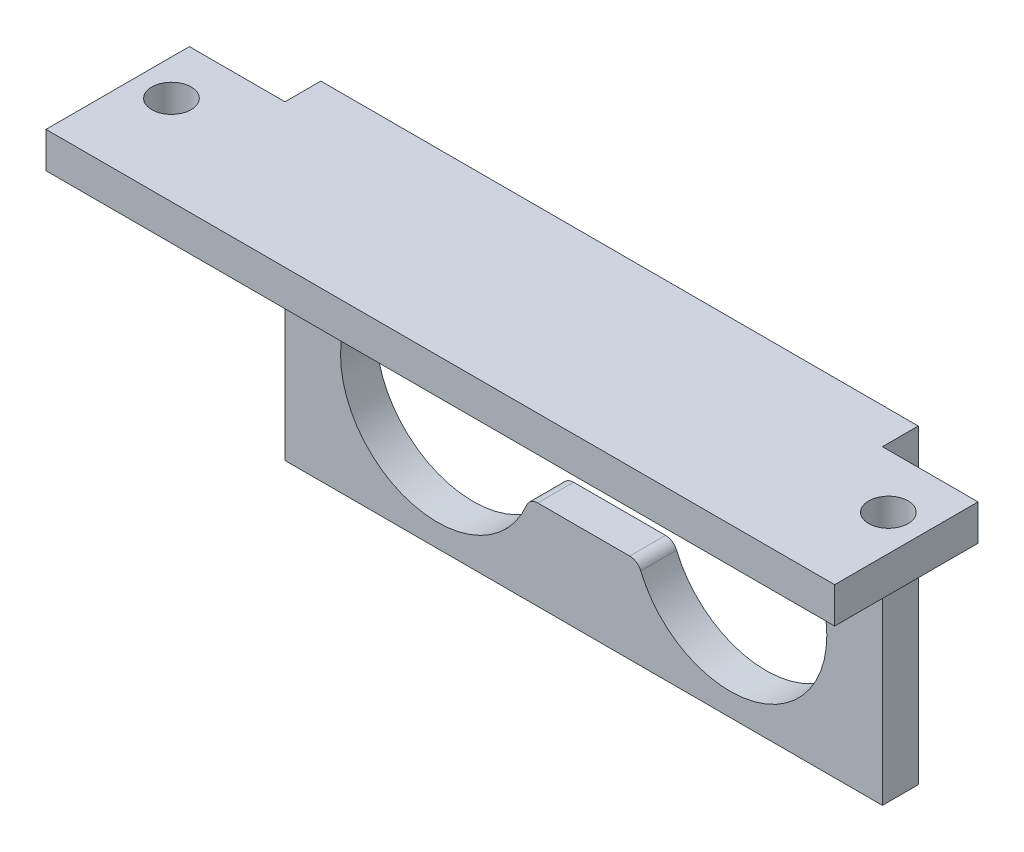
SolidWorks part; units mm, degrees
ref_plane "前视基准面" through (0, 0, 0) normal (0, 0, 1) x (1, 0, 0)
ref_plane "上视基准面" through (0, 0, 0) normal (0, 1, 0) x (1, 0, 0)
ref_plane "右视基准面" through (0, 0, 0) normal (1, 0, 0) x (0, 0, -1)
sketch "草图1" plane through (0, 0, 0) normal (0, 0, 1) x (1, 0, 0)
  line L1 (25, -10) -> (-25, -10)
  line L2 (25, -10) -> (25, 10)
  line L3 (25, 10) -> (-25, 10)
  line L4 (-25, -10) -> (-25, 10)
  line L5 (25, -10) -> (-25, 10) construction
  line L6 (25, 10) -> (-25, -10) construction
  line L8 (-3.85, 2.5) -> (3.85, 2.5)
  line L9 (3.85, -2.5) -> (-3.85, -2.5)
  line L10 (3.25, 7.25) -> (-3.25, 7.25) construction
  line L11 (3.25, 5.5) -> (-3.25, 5.5)
  line L12 (3.25, 9) -> (-3.25, 9)
  arc A7 (4.7731, -3.1154) -> (4.7731, 3.1154) centre (12.25, 0) ccw
  arc A8 (-4.7731, 3.1154) -> (-4.7731, -3.1154) centre (-12.25, 0) ccw
  arc A9 (3.85, -2.5) -> (4.7731, -3.1154) centre (3.85, -3.5) cw
  arc A10 (3.85, 2.5) -> (4.7731, 3.1154) centre (3.85, 3.5) ccw
  arc A11 (-3.85, -2.5) -> (-4.7731, -3.1154) centre (-3.85, -3.5) ccw
  arc A12 (-3.85, 2.5) -> (-4.7731, 3.1154) centre (-3.85, 3.5) cw
  arc A13 (3.25, 5.5) -> (3.25, 9) centre (3.25, 7.25) ccw
  arc A14 (-3.25, 9) -> (-3.25, 5.5) centre (-3.25, 7.25) ccw
  point P0 (0, 0)
  point P22 (0, 7.25)
  dimension "D3" = 1
  dimension "D4" = 8.1
  dimension "D5" = 8.1
  dimension "D6" = 2.5
  dimension "D8" = 12.25
  dimension "D9" = 12.25
  dimension "D12" = 1.75
  dimension "D1" = 20
  dimension "D2" = 50
  dimension "D7" = 2.5
  dimension "D10" = 7.25
  dimension "D11" = 6.5
  dimension "D13" = 3.25
extrude "凸台-拉伸1" add sketch "草图1" along normal blind 3
sketch "草图2" plane through (0, 10, 0) normal (0, 1, 0) x (1, 0, 0)
  line L1 (-25, 0) -> (25, 0)
  line L2 (-25, 0) -> (-25, -15)
  line L3 (-25, -15) -> (25, -15)
  line L4 (25, 0) -> (25, -15)
  dimension "D1" = 15
extrude "凸台-拉伸2" add sketch "草图2" along normal blind 6
sketch "草图5" plane through (0, 10, 0) normal (0, -1, 0) x (1, 0, 0)
  line L1 (25, 3) -> (-25, 3)
  line L2 (25, 3) -> (25, 15)
  line L3 (25, 15) -> (-25, 15)
  line L4 (-25, 3) -> (-25, 15)
extrude "切除-拉伸2" cut sketch "草图5" against normal blind 3
sketch "草图6" plane through (0, 16, 0) normal (0, 1, 0) x (1, 0, 0)
  line L1 (25, -15) -> (33, -15)
  line L2 (25, -15) -> (25, -3)
  line L3 (25, -3) -> (33, -3)
  line L4 (33, -15) -> (33, -3)
  line L5 (-25, -15) -> (-33, -15)
  line L6 (-25, -15) -> (-25, -3)
  line L7 (-25, -3) -> (-33, -3)
  line L8 (-33, -15) -> (-33, -3)
  circle A0 centre (30, -7.5) radius 1.65
  circle A1 centre (-30, -7.5) radius 1.65
  dimension "D5" = 3.3
  dimension "D6" = 3.3
  dimension "D1" = 12
  dimension "D2" = 8
  dimension "D3" = 8
  dimension "D4" = 12
extrude "凸台-拉伸3" add sketch "草图6" against normal blind 3
